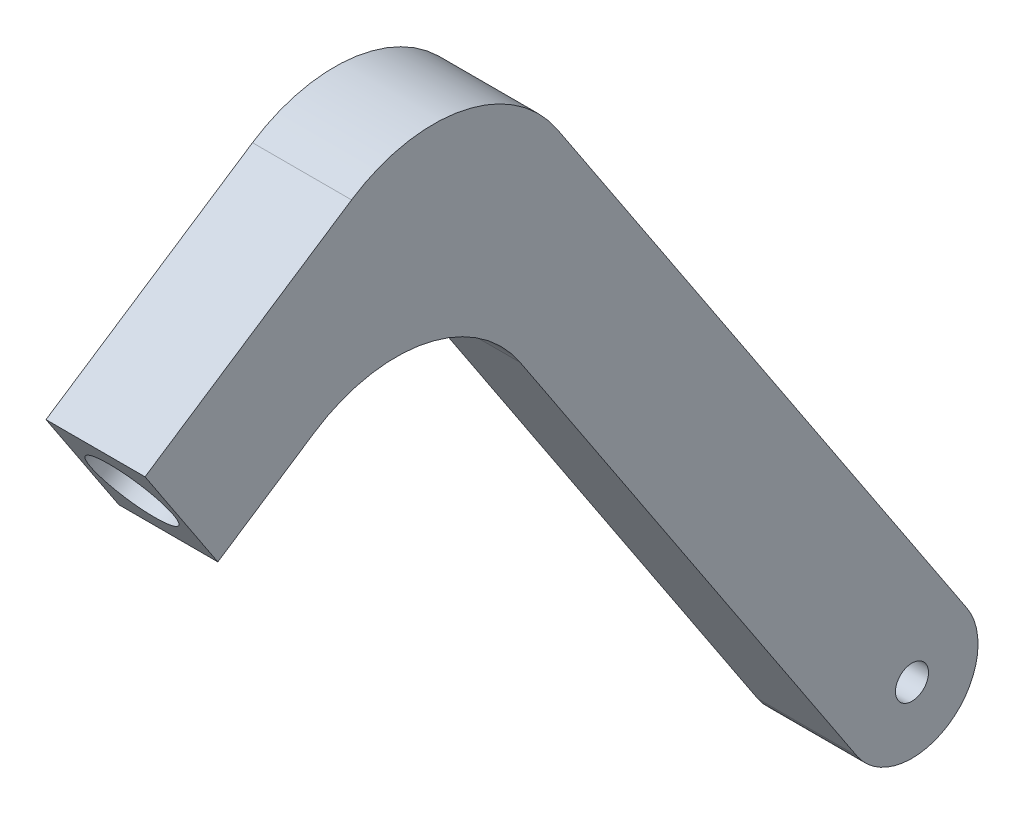
SolidWorks part; units mm, degrees
ref_plane "Front Plane" through (0, 0, 0) normal (0, 0, 1) x (1, 0, 0)
ref_plane "Top Plane" through (0, 0, 0) normal (0, 1, 0) x (1, 0, 0)
ref_plane "Right Plane" through (0, 0, 0) normal (1, 0, 0) x (0, 0, -1)
sketch "Sketch1" plane through (0, 0, 0) normal (1, 0, 0) x (0, 0, -1)
  line L0 (0, 0) -> (-137.9028, 208.5253) construction
  line L1 (-137.9028, 208.5253) -> (-221.3129, 153.3642) construction
  line L2 (16.682, 11.0322) -> (-107.4305, 198.705)
  line L3 (-169.7876, 211.4171) -> (-232.3452, 170.0462)
  line L4 (-16.682, -11.0322) -> (-118.7301, 143.2765)
  line L5 (-181.0872, 155.9886) -> (-210.2807, 136.6822)
  line L6 (16.682, 11.0322) -> (-132.253, 236.2396) construction
  line L7 (-132.253, 236.2396) -> (-232.3452, 170.0462) construction
  line L8 (-16.682, -11.0322) -> (-143.5526, 180.8111) construction
  line L9 (-143.5526, 180.8111) -> (-210.2807, 136.6822) construction
  line L10 (-210.2807, 136.6822) -> (-232.3452, 170.0462)
  arc A0 (16.682, 11.0322) -> (-16.682, -11.0322) centre (0, 0) cw
  arc A2 (-107.4305, 198.705) -> (-169.7876, 211.4171) centre (-144.9651, 173.8825) ccw
  arc A3 (-118.7301, 143.2765) -> (-181.0872, 155.9886) centre (-156.2647, 118.454) ccw
  circle A5 centre (0, 0) radius 5
  dimension "D6" = 45
  dimension "D8" = 10
  dimension "D1" = 90
  dimension "D2" = 250
  dimension "D3" = 100
  dimension "D4" = 20
  dimension "D5" = 20
extrude "Boss-Extrude1" add sketch "Sketch1" along normal blind 30
sketch "Sketch2" plane through (0, -55.1611, 83.4101) normal (0, -0.5516, 0.8341) x (1, 0, 0)
  line L0 (15, 270) -> (15, 230) construction
  line L1 (30, 270) -> (0, 270) construction
  line L2 (30, 230) -> (0, 230) construction
  circle A0 centre (15, 250) radius 12.5
  dimension "D1" = 25
extrude "Cut-Extrude1" cut sketch "Sketch2" against normal blind 20
